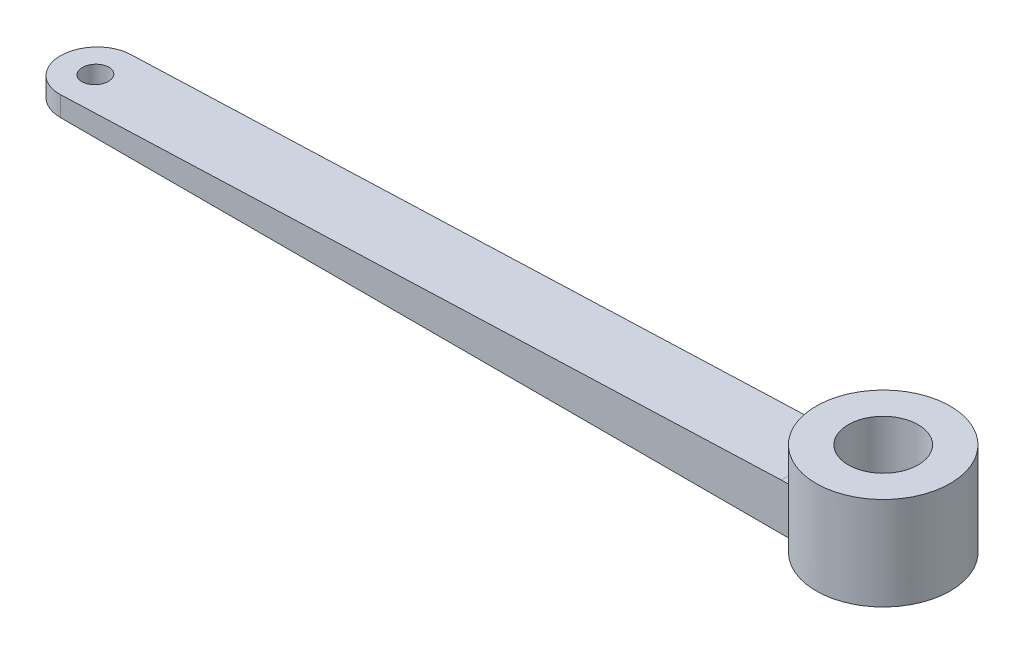
SolidWorks part; units mm, degrees
ref_plane "Front Plane" through (0, 0, 0) normal (0, 0, 1) x (1, 0, 0)
ref_plane "Top Plane" through (0, 0, 0) normal (0, 1, 0) x (1, 0, 0)
ref_plane "Right Plane" through (0, 0, 0) normal (1, 0, 0) x (0, 0, -1)
sketch "Sketch1" plane through (0, 0, 0) normal (0, 1, 0) x (1, 0, 0)
  circle A0 centre (0, 0) radius 9.144
  circle A1 centre (0, 0) radius 4.7625
  dimension "D1" = 18.288
  dimension "D2" = 9.525
extrude "Boss-Extrude1" add sketch "Sketch1" along normal blind 12.7
sketch "Sketch2" plane through (0, 0, 0) normal (0, 1, 0) x (1, 0, 0)
  line L1 (0, 4.7625) -> (-112.268, 4.7625)
  line L2 (0, 4.7625) -> (0, -4.7625)
  line L3 (0, -4.7625) -> (-112.268, -4.7625)
  line L4 (-112.268, 4.7625) -> (-112.268, -4.7625)
  circle A0 centre (0, 0) radius 4.7625 construction
  circle A1 centre (-107.442, 0) radius 1.778
  arc A2 (-107.442, -4.7625) -> (-107.442, 4.7625) centre (-107.442, 0) cw
  dimension "D3" = 3.556
  dimension "D5" = 4.7625
  dimension "D1" = 9.525
  dimension "D2" = 112.268
  dimension "D4" = 4.826
extrude "Boss-Extrude2" add sketch "Sketch2" along normal blind 6.35 contours A2 L3 L2 L1 A1
sketch "Sketch3" plane through (0, 12.7, 0) normal (0, 1, 0) x (1, 0, 0)
  circle A0 centre (0, 0) radius 4.7625
extrude "Cut-Extrude1" cut sketch "Sketch3" against normal blind 13.97
sketch "Sketch4" plane through (0, 0, 0) normal (0, 0, 1) x (1, 0, 0)
  line L0 (-112.2045, 0) -> (-112.2045, 2.54)
  line L1 (-112.2045, 6.35) -> (-112.2045, 0) construction
  line L2 (-112.2045, 2.54) -> (-9.144, 6.35)
  line L3 (-9.144, 6.35) -> (-9.144, 0)
  line L4 (-7.8059, 0) -> (-107.442, 0) construction
  line L5 (-9.144, 0) -> (-112.2045, 0)
  line L6 (-112.2045, 6.35) -> (-9.144, 6.35)
  line L7 (-112.2045, 2.54) -> (-112.2045, 6.35)
  line L8 (-112.2045, 6.35) -> (-9.144, 6.35)
  line L9 (-9.144, 6.35) -> (-112.2045, 2.54)
  dimension "D1" = 2.54
extrude "Cut-Extrude3" cut sketch "Sketch4" against normal through all both and the other way through all contours L7 L2 L6
